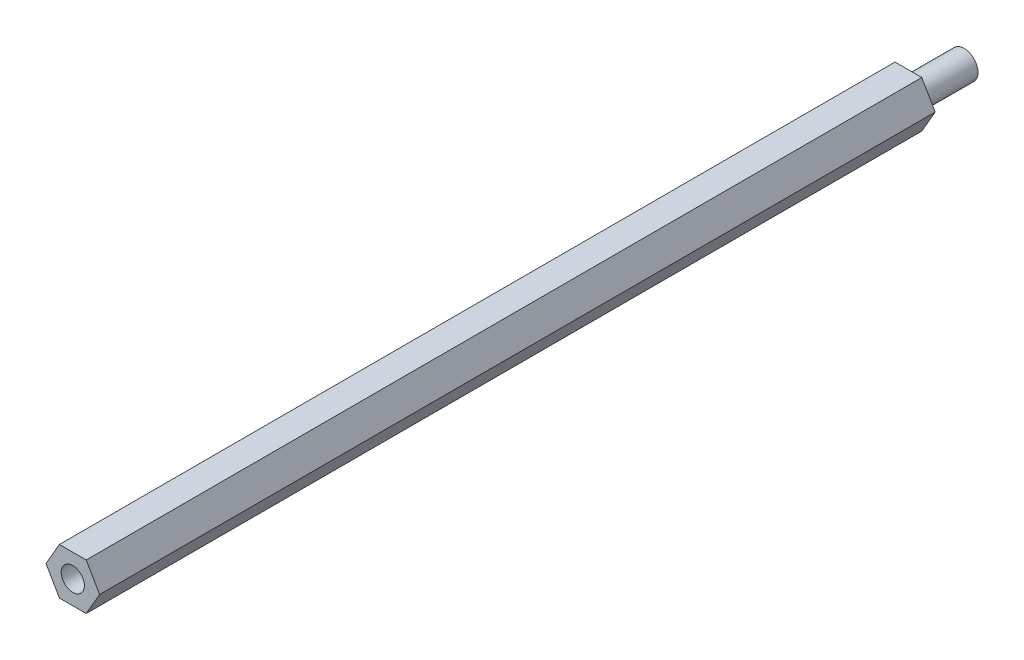
SolidWorks part; units mm, degrees
material "黃銅"
ref_plane "前基準面" through (0, 0, 0) normal (0, 0, 1) x (1, 0, 0)
ref_plane "上基準面" through (0, 0, 0) normal (0, 1, 0) x (1, 0, 0)
ref_plane "右基準面" through (0, 0, 0) normal (1, 0, 0) x (0, 0, -1)
sketch "草圖1" plane through (0, 0, 0) normal (0, 0, 1) x (1, 0, 0)
  line L1 (-1.4434, 2.5) -> (-2.8868, 0)
  line L2 (-2.8868, 0) -> (-1.4434, -2.5)
  line L3 (-1.4434, -2.5) -> (1.4434, -2.5)
  line L4 (1.4434, -2.5) -> (2.8868, 0)
  line L5 (2.8868, 0) -> (1.4434, 2.5)
  line L6 (1.4434, 2.5) -> (-1.4434, 2.5)
  circle A0 centre (0, 0) radius 2.5 construction
  dimension "D1" = 5
extrude "填料-伸長1" add sketch "草圖1" along normal blind 90
sketch "草圖4" plane through (0, 0, 0) normal (0, 0, -1) x (-1, 0, 0)
  circle A0 centre (0, 0) radius 1.5
  dimension "D1" = 3
extrude "填料-伸長2" add sketch "草圖4" along normal blind 6
hole_wizard "M3x0.5 螺紋孔1" positions "草圖2" profile "草圖3" tap size "M3x0.5" standard "Ansi Metric"
sketch "草圖2" plane through (0, 0, 90) normal (0, 0, 1) x (1, 0, 0)
  point P0 (0, 0)
sketch "草圖3" plane through (0, 0, 90) normal (1, 0, 0) x (0, -1, 0)
  line L0 (0, 0) -> (0, 8.2511)
  line L1 (0, 8.2511) -> (1.25, 7.5)
  line L2 (1.25, 7.5) -> (1.25, 0)
  line L5 (1.25, 0) -> (0, 0)
  line L10 (0, 8.2511) -> (-1.25, 7.5) construction
  line L11 (0, -6.35) -> (0, 107.95) construction
  dimension "螺孔鑽直徑" = 2.5
  dimension "螺孔鑽深度" = 7.5
  dimension "導頭角度" = 118
